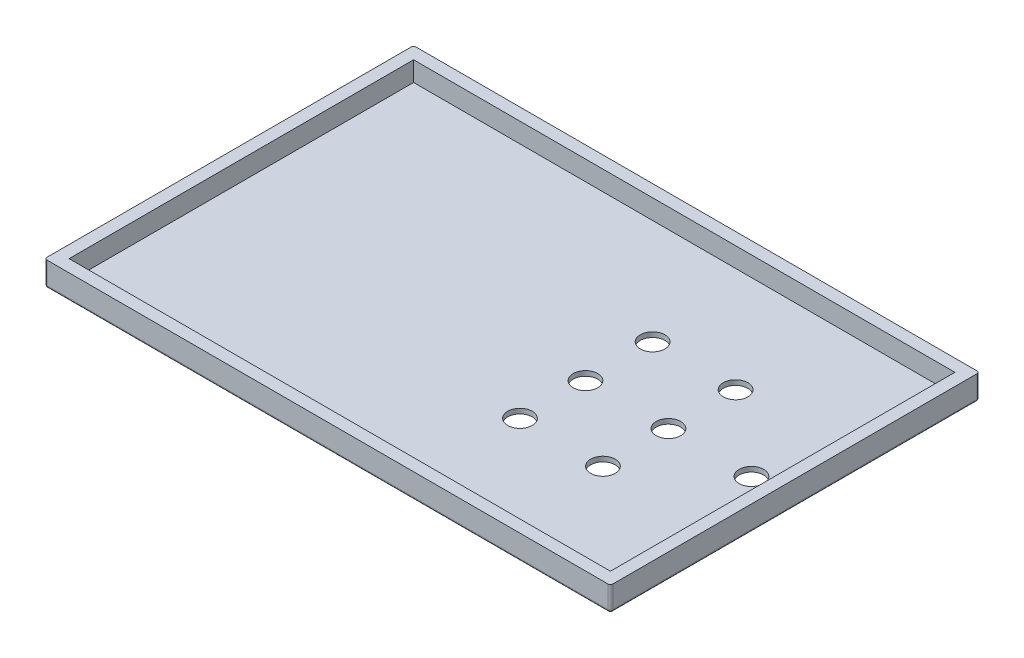
SolidWorks part; units mm, degrees
ref_plane "Front Plane" through (0, 0, 0) normal (0, 0, 1) x (1, 0, 0)
ref_plane "Top Plane" through (0, 0, 0) normal (0, 1, 0) x (1, 0, 0)
ref_plane "Right Plane" through (0, 0, 0) normal (1, 0, 0) x (0, 0, -1)
sketch "Sketch1" plane through (0, 0, 0) normal (0, 1, 0) x (1, 0, 0)
  line L1 (0, 0) -> (230, 0)
  line L2 (0, 0) -> (0, 150)
  line L3 (0, 150) -> (230, 150)
  line L4 (230, 0) -> (230, 150)
  line L5 (0, 0) -> (230, 150) construction
  line L6 (0, 150) -> (230, 0) construction
  point P4 (115, 75)
extrude "Boss-Extrude3" add sketch "Sketch1" along normal blind 10
sketch "Sketch3" plane through (0, 10, 0) normal (0, 1, 0) x (1, 0, 0)
  line L3 (4.9838, 145.0119) -> (225.0162, 145.0119)
  line L4 (4.9838, 145.0119) -> (4.9838, 4.9881)
  line L5 (4.9838, 4.9881) -> (225.0162, 4.9881)
  line L6 (225.0162, 145.0119) -> (225.0162, 4.9881)
  line L7 (115, 4.9881) -> (115, 145.0119) construction
  line L8 (4.9838, 75) -> (225.0162, 75) construction
  point P4 (115, 75)
extrude "Cut-Extrude1" cut sketch "Sketch3" against normal blind 8
fillet "Fillet1" radius 1 1 edges at (0, 5, 0)
fillet "Fillet2" radius 1 3 edges at (0, 5, -150) (230, 5, 0) (230, 5, -150)
fillet "Fillet3" radius 1 8 edges at (229.7071, 0, -149.7071) (230, 0, -75) (229.7071, 0, -0.2929) (115, 0, 0) (0.2929, 0, -0.2929) (0, 0, -75) (0.2929, 0, -149.7071) (115, 0, -150)
sketch "Sketch6" plane through (0, 0, 0) normal (0, -1, 0) x (1, 0, 0)
  line L0 (229, -75) -> (1, -75)
  line L1 (229, -149) -> (229, -1) construction
  line L2 (1, -1) -> (1, -149) construction
  line L9 (144.8625, -75) -> (212.3226, -75) construction
  circle A0 centre (144.8265, -48.4085) radius 5
  circle A1 centre (178.5566, -48.4085) radius 5
  circle A2 centre (178.5926, -75) radius 5
  circle A3 centre (144.8625, -75) radius 5
  circle A4 centre (144.8625, -102.2901) radius 5
  circle A5 centre (178.5926, -102.2901) radius 5
  circle A6 centre (212.3226, -75) radius 5
  point P6 (178.5926, -75)
extrude "Cut-Extrude3" cut sketch "Sketch6" against normal blind 10 contours A0 | A1 | A6 | A2 | A3 | A5 | A4
